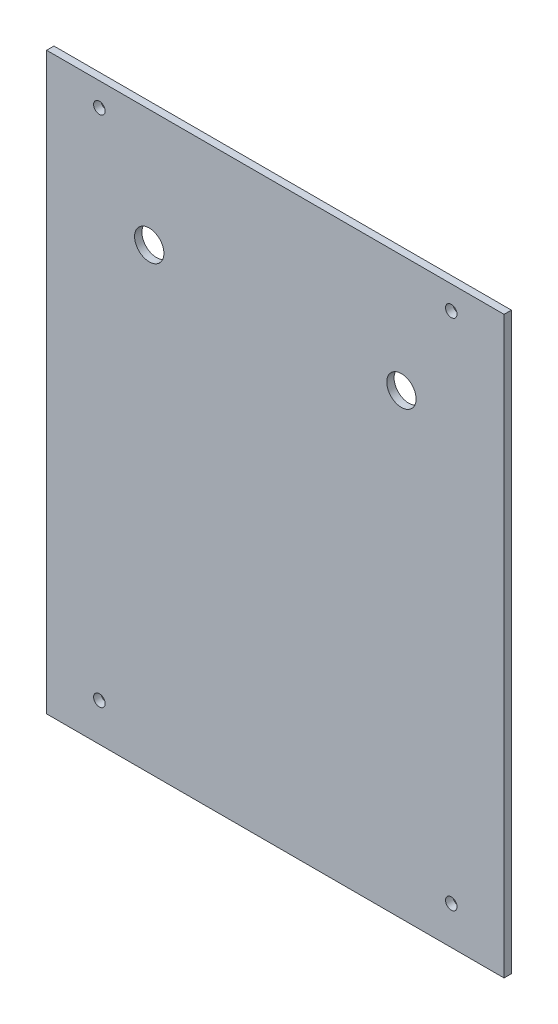
SolidWorks part; units mm, degrees
ref_plane "Front Plane" through (0, 0, 0) normal (0, 0, 1) x (1, 0, 0)
ref_plane "Top Plane" through (0, 0, 0) normal (0, 1, 0) x (1, 0, 0)
ref_plane "Right Plane" through (0, 0, 0) normal (1, 0, 0) x (0, 0, -1)
sketch "Sketch1" plane through (0, 0, 0) normal (0, 0, 1) x (1, 0, 0)
  line L0 (-101.6, -279.4) -> (-101.6, 152.4) construction
  line L1 (101.6, -25.4) -> (-101.6, -25.4) construction
  line L2 (190.5, -279.4) -> (-190.5, -279.4) construction
  line L3 (101.6, 152.4) -> (101.6, -279.4) construction
  line L4 (-101.6, -279.4) -> (-101.6, -25.4) construction
  line L5 (101.6, -25.4) -> (-101.6, -25.4) construction
  line L6 (101.6, -279.4) -> (-101.6, -279.4) construction
  line L7 (101.6, -25.4) -> (101.6, -279.4) construction
  line L8 (99.06, -276.86) -> (-99.06, -276.86)
  line L9 (-99.06, -276.86) -> (-99.06, -27.94)
  line L10 (99.06, -27.94) -> (-99.06, -27.94)
  line L11 (99.06, -27.94) -> (99.06, -276.86)
  circle A0 centre (-76.2, -260.35) radius 2.5 construction
  circle A1 centre (-76.2, -38.1) radius 2.5 construction
  circle A2 centre (76.2, -38.1) radius 2.5 construction
  circle A3 centre (76.2, -260.35) radius 2.5 construction
  circle A4 centre (-76.2, -260.35) radius 2.5
  circle A5 centre (-76.2, -38.1) radius 2.5
  circle A6 centre (76.2, -38.1) radius 2.5
  circle A7 centre (76.2, -260.35) radius 2.5
  dimension "D1" = 2.54
extrude "Boss-Extrude1" add sketch "Sketch1" along normal blind 3.175
sketch "Sketch2" plane through (0, 0, 3.175) normal (0, 0, 1) x (1, 0, 0)
  line L0 (99.06, -27.94) -> (-99.06, -27.94) construction
  line L1 (-99.06, -27.94) -> (-99.06, -276.86) construction
  line L2 (0, -27.94) -> (0, -48.4438) construction
  circle A0 centre (-54.61, -78.74) radius 6.35
  circle A1 centre (54.61, -78.74) radius 6.35
  dimension "D1" = 12.7
  dimension "D2" = 50.8
  dimension "D3" = 44.45
extrude "Cut-Extrude1" cut sketch "Sketch2" against normal through all
